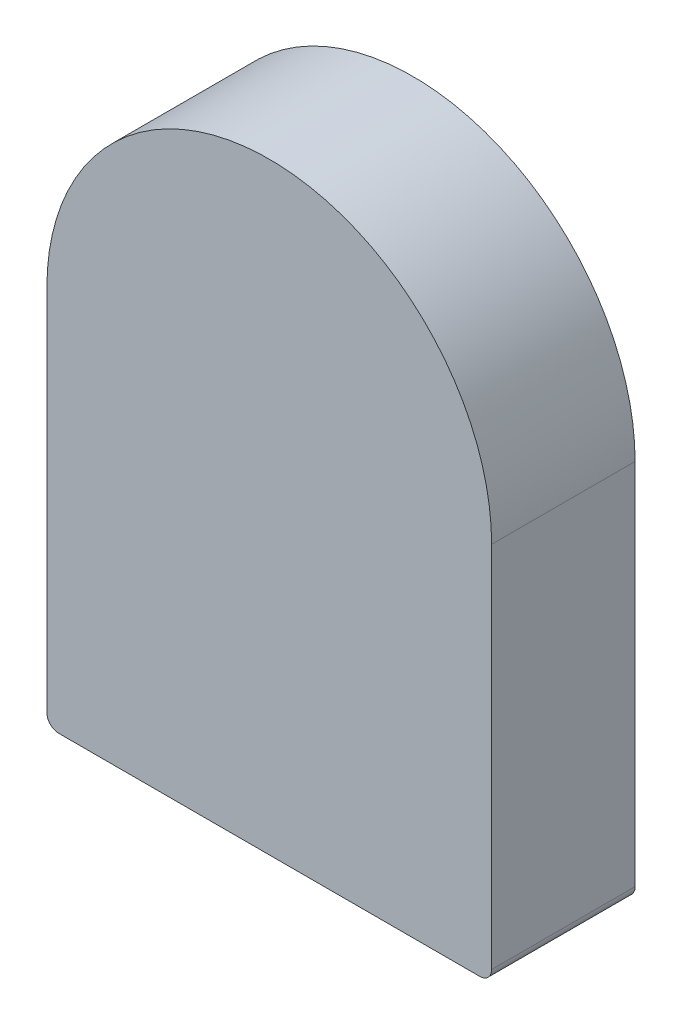
SolidWorks part; units mm, degrees
ref_plane "前视基准面" through (0, 0, 0) normal (0, 0, 1) x (1, 0, 0)
ref_plane "上视基准面" through (0, 0, 0) normal (0, 1, 0) x (1, 0, 0)
ref_plane "右视基准面" through (0, 0, 0) normal (1, 0, 0) x (0, 0, -1)
other "Configuration Table"
sketch "草图1" plane through (0, 0, 0) normal (0, 0, 1) x (1, 0, 0)
  line L2 (-9.3, 0) -> (-9.3, -15.9)
  line L3 (-9.3, -15.9) -> (9.3, -15.9)
  line L4 (9.3, 0) -> (9.3, -15.9)
  arc A0 (9.3, 0) -> (-9.3, 0) centre (0, 0) ccw
  dimension "D1" = 9.3
  dimension "D2" = 15.9
extrude "凸台-拉伸1" add sketch "草图1" along normal blind 6
fillet "圆角1" radius 0.5 2 edges at (9.3, -15.9, 3) (-9.3, -15.9, 3)
